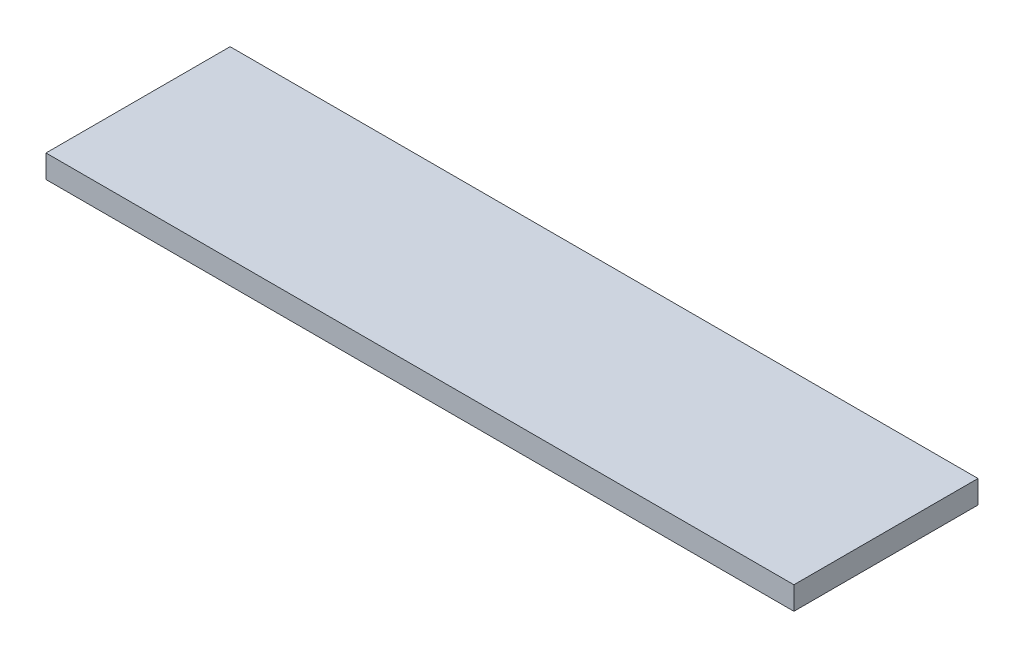
SolidWorks part; units mm, degrees
material "Kupfer"
ref_plane "Ebene vorne" through (0, 0, 0) normal (0, 0, 1) x (1, 0, 0)
ref_plane "Ebene oben" through (0, 0, 0) normal (0, 1, 0) x (1, 0, 0)
ref_plane "Ebene rechts" through (0, 0, 0) normal (1, 0, 0) x (0, 0, -1)
sketch "Skizze1" plane through (0, 0, 0) normal (0, 1, 0) x (1, 0, 0)
  line L1 (0, 0) -> (32.5, 0)
  line L2 (0, 0) -> (0, 8)
  line L3 (0, 8) -> (32.5, 8)
  line L4 (32.5, 0) -> (32.5, 8)
  dimension "D1" = 32.5
  dimension "D2" = 8
extrude "Aufsatz-Linear austragen1" add sketch "Skizze1" along normal blind 1
sketch "Skizze2" plane through (0, 0, 0) normal (0, -1, 0) x (1, 0, 0)
  line L0 (0, 0) -> (32.5, 0) construction
  line L1 (32.5, -8) -> (0, -8) construction
  line L2 (0, -8) -> (0, 0) construction
  circle A0 centre (4, -4) radius 4
